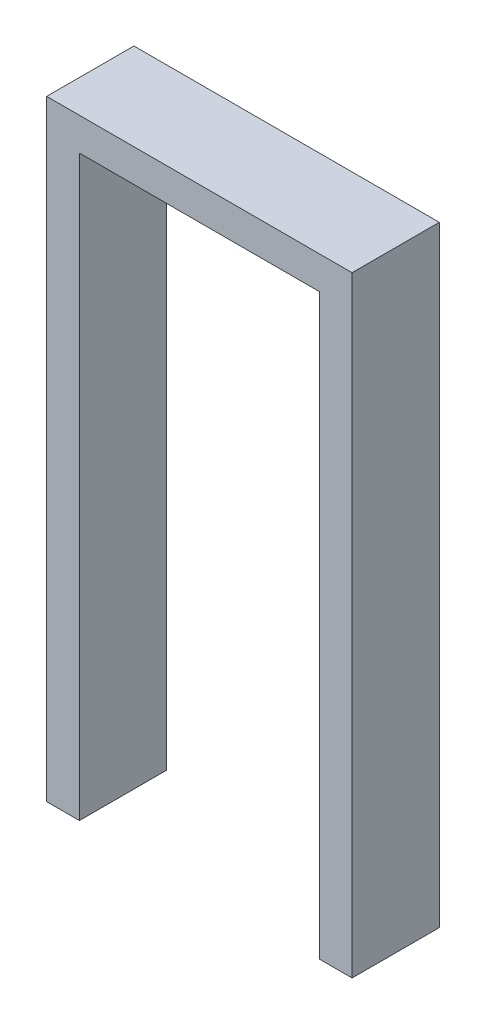
SolidWorks part; units mm, degrees
ref_plane "Front Plane" through (0, 0, 0) normal (0, 0, 1) x (1, 0, 0)
ref_plane "Top Plane" through (0, 0, 0) normal (0, 1, 0) x (1, 0, 0)
ref_plane "Right Plane" through (0, 0, 0) normal (1, 0, 0) x (0, 0, -1)
sketch "Sketch1" plane through (0, 0, 0) normal (0, 0, 1) x (1, 0, 0)
  line L0 (317.5, 38.1) -> (317.5, -673.1)
  line L1 (0, 0) -> (279.4, 0)
  line L2 (0, 0) -> (0, -673.1)
  line L4 (279.4, 0) -> (279.4, -673.1)
  line L6 (0, -673.1) -> (0, -609.6)
  line L10 (279.4, -673.1) -> (279.4, -609.6)
  line L13 (-38.1, 38.1) -> (317.5, 38.1)
  line L14 (-38.1, 38.1) -> (-38.1, -673.1)
  line L15 (-38.1, -673.1) -> (0, -673.1)
  line L16 (317.5, -673.1) -> (279.4, -673.1)
  point P8 (0, 0)
  dimension "D1" = 279.4
  dimension "D2" = 673.1
  dimension "D5" = 38.1
extrude "Boss-Extrude1" add sketch "Sketch1" along normal blind 101.6 contours L16 L0 L13 L14 L15 L2 L1 L4
